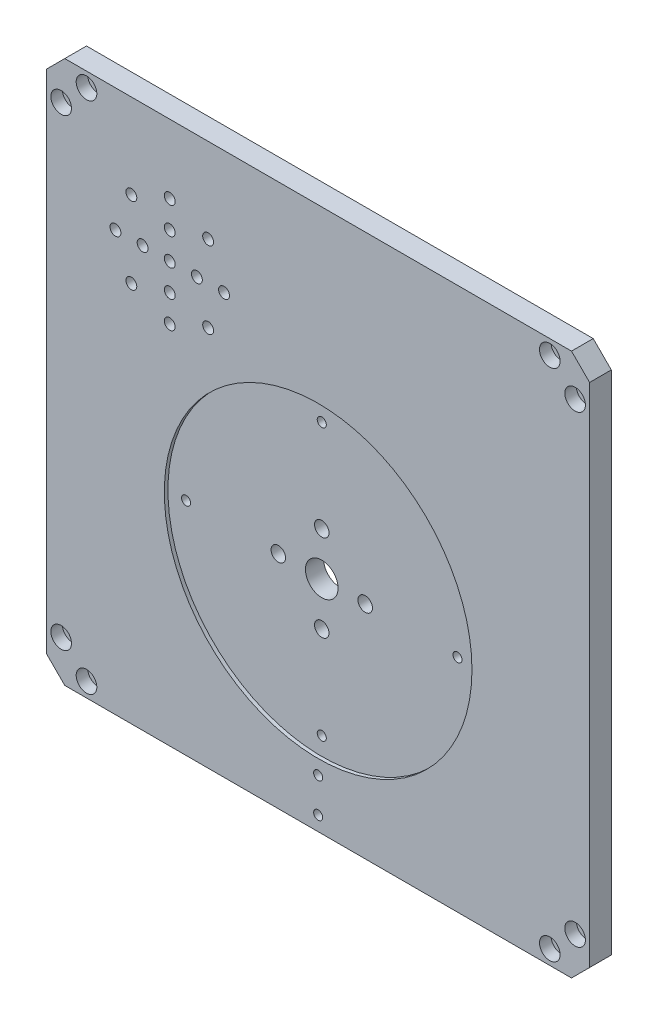
SolidWorks part; units mm, degrees
ref_plane "前视基准面" through (0, 0, 0) normal (0, 0, 1) x (1, 0, 0)
ref_plane "上视基准面" through (0, 0, 0) normal (0, 1, 0) x (1, 0, 0)
ref_plane "右视基准面" through (0, 0, 0) normal (1, 0, 0) x (0, 0, -1)
sketch "草图1" plane through (0, 0, 0) normal (0, 0, 1) x (1, 0, 0)
  line L1 (75, -75) -> (-75, -75)
  line L2 (75, -75) -> (75, 75)
  line L3 (75, 75) -> (-75, 75)
  line L4 (-75, -75) -> (-75, 75)
  line L5 (75, -75) -> (-75, 75) construction
  line L6 (75, 75) -> (-75, -75) construction
  point P0 (0, 0)
  dimension "D1" = 150
  dimension "D2" = 150
extrude "凸台-拉伸1" add sketch "草图1" along normal blind 6
sketch "草图2" plane through (0, 0, 6) normal (0, 0, 1) x (1, 0, 0)
  line L0 (-128.658, 0) -> (125.3726, 0) construction
  line L1 (0, 106.4843) -> (0, -107.9786) construction
  line L2 (-75, -75) -> (75, -75) construction
  circle A0 centre (0, -15) radius 42.5
  dimension "D1" = 85
  dimension "D2" = 60
extrude "切除-拉伸1" cut sketch "草图2" against normal blind 1
chamfer "倒角1" distance 5 angle 45 4 edges at (-75, -75, 3) (75, -75, 3) (75, 75, 3) (-75, 75, 3)
sketch "草图4" plane through (0, 0, 6) normal (0, 0, 1) x (1, 0, 0)
  line L0 (70, 75) -> (-70, 75) construction
  line L1 (75, -70) -> (75, 70) construction
  circle A0 centre (64, 71) radius 1.5
  circle A1 centre (71, 64) radius 1.5
  dimension "D1" = 3
  dimension "D2" = 3
  dimension "D3" = 4
  dimension "D4" = 11
  dimension "D5" = 11
  dimension "D6" = 4
extrude "切除-拉伸3" cut sketch "草图4" against normal blind 10
sketch "草图5" plane through (0, 0, 6) normal (0, 0, 1) x (1, 0, 0)
  line L0 (70, 75) -> (-70, 75) construction
  line L1 (75, -70) -> (75, 70) construction
  circle A0 centre (64, 71) radius 2.85
  circle A1 centre (71, 64) radius 2.85
  dimension "D1" = 5.7
  dimension "D2" = 5.7
  dimension "D3" = 4
  dimension "D4" = 11
  dimension "D5" = 4
  dimension "D6" = 11
extrude "切除-拉伸4" cut sketch "草图5" against normal blind 3.2
sketch "草图6" plane through (0, 0, 6) normal (0, 0, 1) x (1, 0, 0)
  line L0 (70, 75) -> (-70, 75) construction
  line L1 (-75, 70) -> (-75, -70) construction
  circle A0 centre (-64, 71) radius 1.5
  circle A1 centre (-71, 64) radius 1.5
  dimension "D1" = 3
  dimension "D2" = 3
  dimension "D3" = 4
  dimension "D4" = 11
  dimension "D5" = 4
  dimension "D6" = 11
extrude "切除-拉伸5" cut sketch "草图6" against normal blind 10
sketch "草图7" plane through (0, 0, 6) normal (0, 0, 1) x (1, 0, 0)
  circle A0 centre (-64, 71) radius 2.85
  circle A1 centre (-71, 64) radius 2.85
  dimension "D1" = 5.7
extrude "切除-拉伸6" cut sketch "草图7" against normal blind 3.2
mirror "镜向1" about plane through (0, 0, 0) normal (0, 1, 0) of "切除-拉伸3", "切除-拉伸4", "切除-拉伸5", "切除-拉伸6"
sketch "草图8" plane through (0, 0, 5) normal (0, 0, 1) x (1, 0, 0)
  circle A0 centre (0, -15) radius 4.5
  circle A2 centre (0, -15) radius 42.5 construction
  dimension "D1" = 9
extrude "切除-拉伸7" cut sketch "草图8" against normal blind 10
sketch "草图9" plane through (0, 0, 5) normal (0, 0, 1) x (1, 0, 0)
  line L0 (-75, -15) -> (75, -15) construction
  line L1 (-70, -75) -> (70, -75) construction
  line L2 (-75, 70) -> (-75, -70) construction
  line L3 (75, -70) -> (75, 70) construction
  line L4 (0, -15) -> (0, -43.1602) construction
  line L5 (0, -15) -> (0, 16.9417) construction
  circle A0 centre (-12, -15) radius 2
  circle A1 centre (12, -15) radius 2
  circle A4 centre (0, -27) radius 2
  circle A5 centre (0, -3) radius 2
  dimension "D2" = 4
  dimension "D3" = 4
  dimension "D4" = 24
  dimension "D5" = 12
  dimension "D6" = 4
  dimension "D8" = 4
  dimension "D9" = 12
  dimension "D1" = 60
  dimension "D7" = 12
extrude "切除-拉伸8" cut sketch "草图9" against normal blind 10
sketch "草图10" plane through (0, 0, 5) normal (0, 0, 1) x (1, 0, 0)
  line L0 (0, -15) -> (0, 133.0824) construction
  circle A0 centre (0, -15) radius 37.5 construction
  circle A1 centre (0, 22.5) radius 1
  circle A2 centre (37.5, -15) radius 1
  circle A3 centre (0, -52.5) radius 1
  circle A4 centre (-37.5, -15) radius 1
  point P16 (0, -15)
  dimension "D1" = 75
  dimension "D2" = 2
  dimension "D3" = 4
extrude "切除-拉伸9" cut sketch "草图10" against normal blind 10
hole_wizard "M3 螺纹孔1" positions "草图13" profile "草图14" tap size "M3" standard "GB"
sketch "草图13" plane through (0, 0, 5) normal (0, 0, 1) x (1, 0, 0)
  point P0 (0, 22.5)
  point P3 (-37.5, -15)
  point P6 (0, -52.5)
  point P9 (37.5, -15)
sketch "草图14" plane through (0, 22.5, 5) normal (1, 0, 0) x (0, -1, 0)
  line L0 (0, 0) -> (0, 8.2511)
  line L1 (0, 8.2511) -> (1.25, 7.5)
  line L2 (1.25, 7.5) -> (1.25, 0)
  line L5 (1.25, 0) -> (0, 0)
  line L10 (0, 8.2511) -> (-1.25, 7.5) construction
  line L11 (0, -6.35) -> (0, 107.95) construction
  dimension "螺纹孔钻头直径" = 2.5
  dimension "螺纹孔钻头深度" = 7.5
  dimension "导头角度" = 118
cosmetic thread "孔螺蚊线1" parameters "D1"=5, "D2"=3
cosmetic thread "孔螺蚊线2" parameters "D1"=5, "D2"=3
cosmetic thread "孔螺蚊线3" parameters "D1"=5, "D2"=3
cosmetic thread "孔螺蚊线4" parameters "D1"=5, "D2"=3
sketch "草图15" plane through (0, 0, 0) normal (0, 0, -1) x (-1, 0, 0)
  line L0 (75, 70) -> (75, -70) construction
  line L4 (-70, 75) -> (70, 75) construction
  circle A0 centre (41, 41) radius 25.5
  dimension "D1" = 51
  dimension "D2" = 34
  dimension "D3" = 34
extrude "切除-拉伸12" cut sketch "草图15" against normal blind 3
sketch "草图16" plane through (0, 0, 3) normal (0, 0, -1) x (-1, 0, 0)
  circle A0 centre (41, 41) radius 1.5
  circle A1 centre (41, 41) radius 7.5 construction
  circle A2 centre (41, 48.5) radius 1.5
  circle A3 centre (48.5, 41) radius 1.5
  circle A4 centre (41, 33.5) radius 1.5
  circle A5 centre (33.5, 41) radius 1.5
  circle A6 centre (41, 41) radius 15 construction
  circle A7 centre (41, 56) radius 1.5
  circle A8 centre (51.6066, 51.6066) radius 1.5
  circle A9 centre (56, 41) radius 1.5
  circle A10 centre (51.6066, 30.3934) radius 1.5
  circle A11 centre (41, 26) radius 1.5
  circle A12 centre (30.3934, 30.3934) radius 1.5
  circle A13 centre (26, 41) radius 1.5
  circle A14 centre (30.3934, 51.6066) radius 1.5
  point P15 (41, 41)
  point P33 (41, 41)
  dimension "D1" = 3
  dimension "D2" = 15
  dimension "D3" = 3
  dimension "D5" = 30
  dimension "D6" = 3
  dimension "D4" = 4
  dimension "D7" = 8
extrude "切除-拉伸13" cut sketch "草图16" against normal up to surface (3 mm away) up to face at (-68.15, -64, 6)
sketch "草图17" plane through (0, 0, 6) normal (0, 0, 1) x (1, 0, 0)
  line L0 (0, 89.1328) -> (0, -108.6673) construction
  line L1 (-70, -75) -> (70, -75) construction
  circle A0 centre (0, -61.5) radius 1
  circle A1 centre (0, -71) radius 1
  dimension "D1" = 2
  dimension "D2" = 2
  dimension "D3" = 9.5
  dimension "D4" = 4
extrude "切除-拉伸14" cut sketch "草图17" against normal blind 10
hole_wizard "M3 螺纹孔2" positions "草图18" profile "草图19" tap size "M3" standard "GB"
sketch "草图18" plane through (0, 0, 6) normal (0, 0, 1) x (1, 0, 0)
  point P0 (0, -61.5)
  point P3 (0, -71)
sketch "草图19" plane through (0, -61.5, 6) normal (1, 0, 0) x (0, -1, 0)
  line L0 (0, 0) -> (0, 8.2511)
  line L1 (0, 8.2511) -> (1.25, 7.5)
  line L2 (1.25, 7.5) -> (1.25, 0)
  line L5 (1.25, 0) -> (0, 0)
  line L10 (0, 8.2511) -> (-1.25, 7.5) construction
  line L11 (0, -6.35) -> (0, 107.95) construction
  dimension "螺纹孔钻头直径" = 2.5
  dimension "螺纹孔钻头深度" = 7.5
  dimension "导头角度" = 118
cosmetic thread "孔螺蚊线5" parameters "D1"=6, "D2"=3
cosmetic thread "孔螺蚊线6" parameters "D1"=6, "D2"=3
